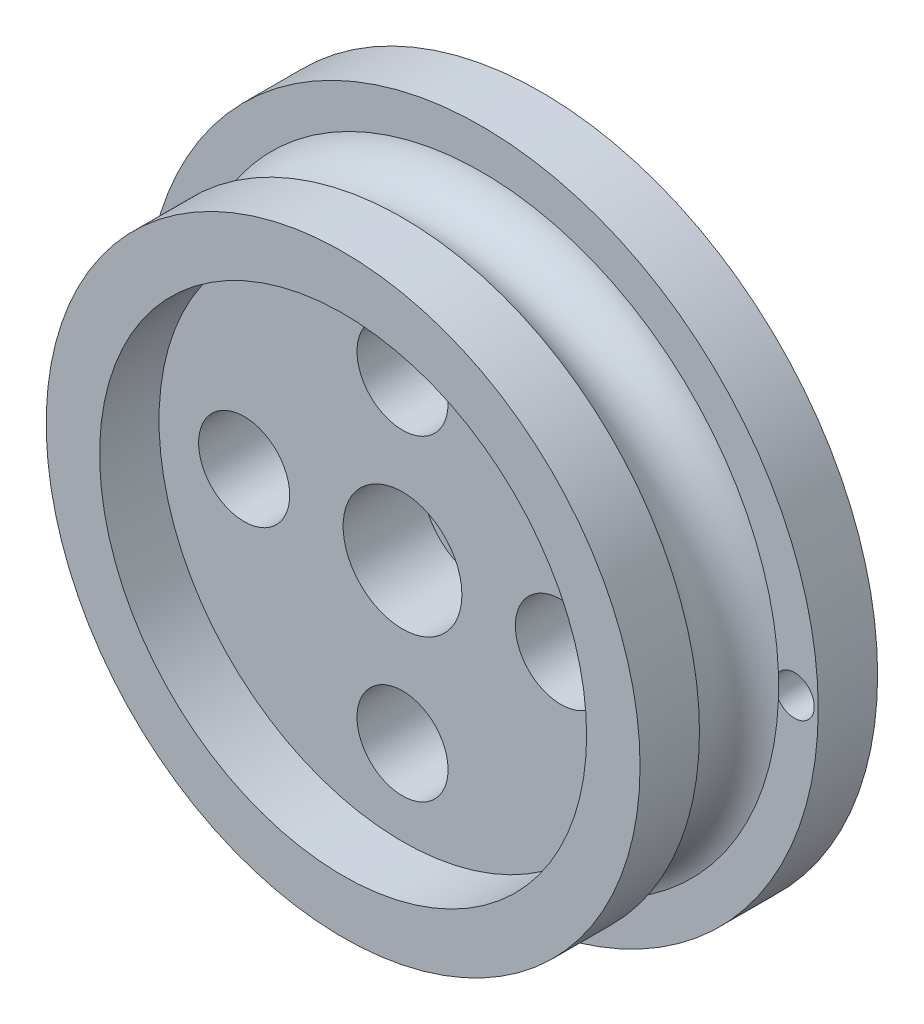
SolidWorks part; units mm, degrees
ref_plane "Front Plane" through (0, 0, 0) normal (0, 0, 1) x (1, 0, 0)
ref_plane "Top Plane" through (0, 0, 0) normal (0, 1, 0) x (1, 0, 0)
ref_plane "Right Plane" through (0, 0, 0) normal (1, 0, 0) x (0, 0, -1)
sketch "Sketch2" plane through (0, 0, 0) normal (0, 0, 1) x (1, 0, 0)
  circle A0 centre (0, 0) radius 15
  circle A1 centre (0, 0) radius 3
  circle A2 centre (-8, 0) radius 2.3
  circle A3 centre (0, 8) radius 2.3
  circle A4 centre (8, 0) radius 2.3
  circle A5 centre (0, -8) radius 2.3
  point P11 (0, 0)
  dimension "D1" = 4.6
  dimension "D2" = 6
  dimension "D3" = 30
  dimension "D4" = 8
extrude "Boss-Extrude1" add sketch "Sketch2" along normal blind 4
sketch "Sketch3" plane through (0, 0, 0) normal (0, 0, 1) x (1, 0, 0)
  line L0 (0, 18.407) -> (0, -24.0857) construction
  circle A0 centre (0, 0) radius 17
  circle A1 centre (0, 0) radius 1.475
  circle A2 centre (-15.8, 0) radius 1
  circle A3 centre (15.8, 0) radius 1
  dimension "D1" = 2
  dimension "D3" = 34
  dimension "D2" = 15.8
extrude "Boss-Extrude2" add sketch "Sketch3" against normal blind 3
sketch "Sketch4" plane through (0, 0, -3) normal (0, 0, -1) x (-1, 0, 0)
  circle A0 centre (0, 0) radius 1.475
  circle A1 centre (0, 0) radius 10
  dimension "D1" = 20
extrude "Boss-Extrude3" [suppressed] add sketch "Sketch4" along normal blind 3.5
sketch "Sketch5" [suppressed] plane through (0, 0, -6.5) normal (0, 0, -1) x (-1, 0, 0)
  line L0 (0, 18.407) -> (0, -24.0857) construction
  circle A0 centre (0, 0) radius 16
  circle A1 centre (0, 0) radius 1.475
  circle A2 centre (-13.2, 0) radius 1
  circle A3 centre (13.2, 0) radius 1
  dimension "D1" = 2
  dimension "D2" = 13.2
extrude "Boss-Extrude4" [suppressed] add sketch "Sketch5" along normal blind 3
sketch "Sketch6" plane through (0, 0, 4) normal (0, 0, 1) x (1, 0, 0)
  circle A0 centre (0, 0) radius 16
  circle A1 centre (0, 0) radius 12.5
  dimension "D1" = 32
  dimension "D2" = 25
sketch "Sketch7" plane through (0, 0, 0) normal (1, 0, 0) x (0, 0, -1)
  line L0 (0, 0) -> (-4, 0) construction
  line L1 (0, 17) -> (0, -17) construction
  line L2 (-4, 16) -> (-4, -16) construction
  line L3 (-4, 15) -> (0, 15)
  arc A0 (-4, 15) -> (0, 15) centre (-2, 15.5906) ccw
  dimension "D1" = 2.0854
revolve "Cut-Revolve1" cut sketch "Sketch7" angle 360 about L0
sketch "Sketch8" plane through (0, 0, 4) normal (0, 0, 1) x (1, 0, 0)
  circle A0 centre (0, 0) radius 15
  circle A1 centre (0, 0) radius 10.3 construction
  circle A2 centre (0, 0) radius 12.3
  dimension "D1" = 30
  dimension "D2" = 20.6
  dimension "D3" = 24.6
extrude "Boss-Extrude5" add sketch "Sketch8" along normal blind 3
